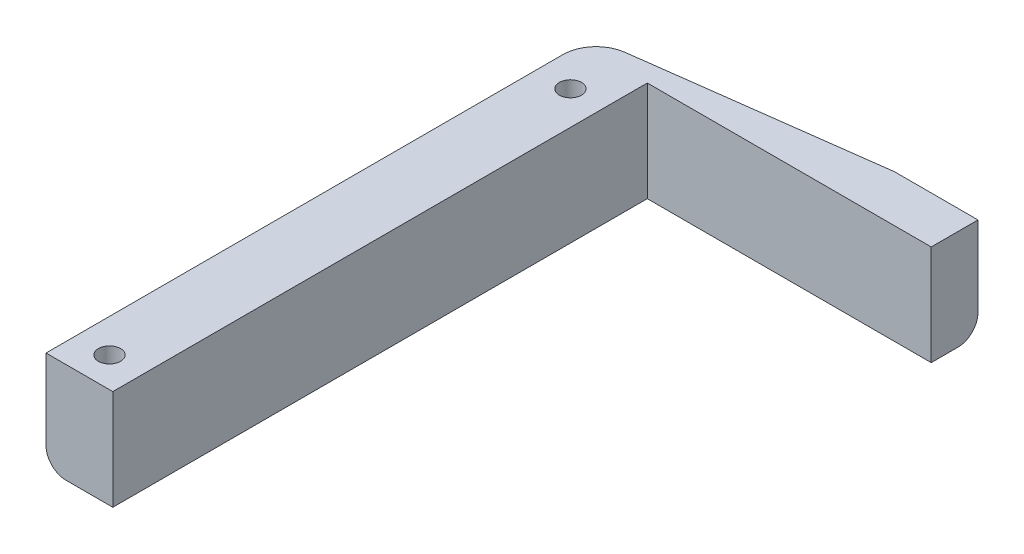
SolidWorks part; units mm, degrees
ref_plane "Front Plane" through (0, 0, 0) normal (0, 0, 1) x (1, 0, 0)
ref_plane "Top Plane" through (0, 0, 0) normal (0, 1, 0) x (1, 0, 0)
ref_plane "Right Plane" through (0, 0, 0) normal (1, 0, 0) x (0, 0, -1)
sketch "Sketch1" plane through (0, 0, 0) normal (0, 1, 0) x (1, 0, 0)
  line L0 (-40.2774, 58.0467) -> (-40.2774, -28.9533)
  line L1 (-40.2774, -28.9533) -> (-30.2774, -28.9533)
  line L2 (-30.2774, -28.9533) -> (-30.2774, 51.0467)
  line L3 (-30.2774, 51.0467) -> (12.2226, 51.0467)
  line L4 (12.2226, 51.0467) -> (12.2226, 58.0467)
  line L5 (12.2226, 58.0467) -> (-40.2774, 58.0467)
  circle A0 centre (-35.2774, -24.4533) radius 1.66
  circle A1 centre (-35.2774, 44.5467) radius 1.66
  dimension "D1" = 3.32
  dimension "D2" = 87
  dimension "D3" = 69
  dimension "D4" = 4.5
  dimension "D5" = 5
  dimension "D6" = 10
  dimension "D7" = 80
  dimension "D8" = 52.5
extrude "Boss-Extrude1" add sketch "Sketch1" along normal blind 15
chamfer "Chamfer1" distance 40 angle 7.5 1 edges at (-40.2774, 7.5, -58.0467)
fillet "Fillet1" radius 5 1 edges at (-40.2774, 7.5, -52.7806)
fillet "Fillet2" radius 3 4 edges at (-39.0366, 0, -51.6924) (-40.2774, 0, -9.7212) (-18.1037, 0, -55.6998) (5.9726, 0, -58.0467)
